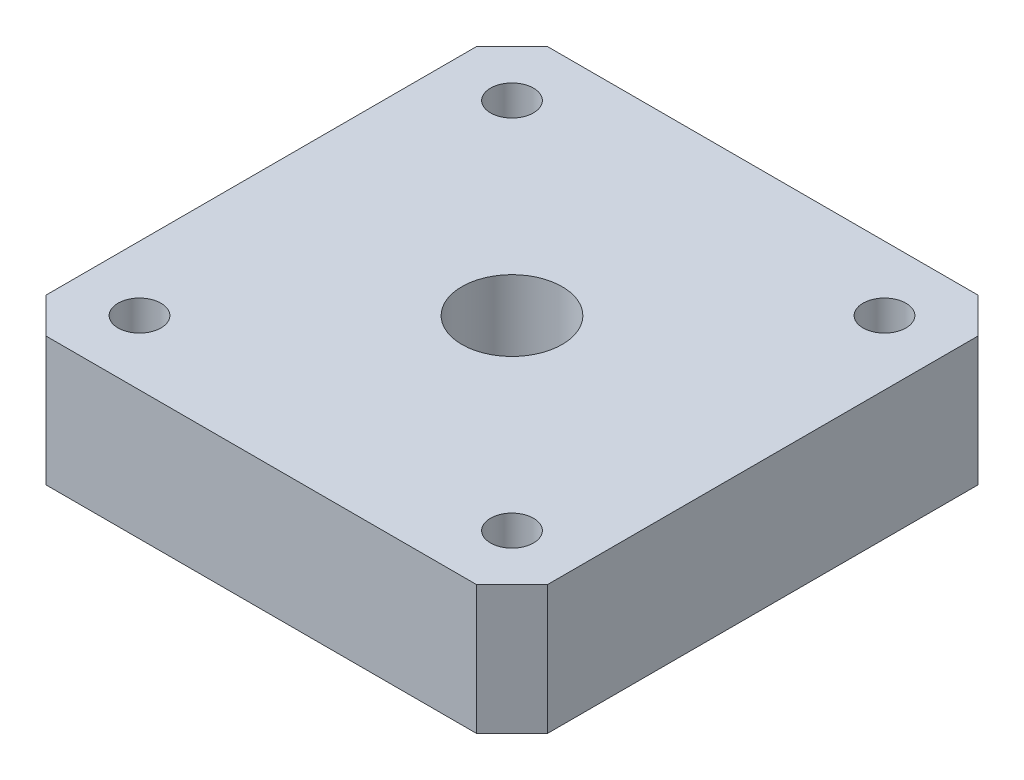
SolidWorks part; units mm, degrees
material "Aleación 1060"
ref_plane "Alzado" through (0, 0, 0) normal (0, 0, 1) x (1, 0, 0)
ref_plane "Planta" through (0, 0, 0) normal (0, 1, 0) x (1, 0, 0)
ref_plane "Vista lateral" through (0, 0, 0) normal (1, 0, 0) x (0, 0, -1)
sketch "Croquis1" plane through (0, 0, 0) normal (0, 1, 0) x (1, 0, 0)
  line L0 (0, 2.4731) -> (2.4731, 0)
  line L1 (2.4731, 0) -> (32.5269, 0)
  line L2 (32.5269, 0) -> (35, 2.4731)
  line L3 (35, 2.4731) -> (35, 32.5269)
  line L4 (35, 32.5269) -> (32.5269, 35)
  line L5 (32.5269, 35) -> (2.4731, 35)
  line L6 (2.4731, 35) -> (0, 32.5269)
  line L7 (0, 32.5269) -> (0, 2.4731)
  dimension "D1" = 35
  dimension "D2" = 35
  dimension "D3" = 46
  dimension "D4" = 46
  dimension "D5" = 45
extrude "Saliente-Extruir1" add sketch "Croquis1" along normal blind 9
sketch "Croquis2" plane through (0, 9, 0) normal (0, 1, 0) x (1, 0, 0)
  line L0 (17.5, 35) -> (17.5, 0) construction
  line L1 (32.5269, 35) -> (2.4731, 35) construction
  line L2 (2.4731, 0) -> (32.5269, 0) construction
  circle A0 centre (17.5, 17.5) radius 3.5
  dimension "D1" = 7
extrude "Cortar-Extruir1" cut sketch "Croquis2" against normal through all
sketch "Croquis3" plane through (0, 9, 0) normal (0, 1, 0) x (1, 0, 0)
  line L0 (4.5, 30.5) -> (30.5, 4.5) construction
  line L1 (4.5, 30.5) -> (30.5, 30.5) construction
  line L2 (4.5, 30.5) -> (4.5, 4.5) construction
  line L3 (4.5, 4.5) -> (30.5, 4.5) construction
  line L4 (30.5, 30.5) -> (30.5, 4.5) construction
  line L5 (4.5, 4.5) -> (30.5, 30.5) construction
  circle A0 centre (4.5, 30.5) radius 1.5
  circle A1 centre (30.5, 30.5) radius 1.5
  circle A2 centre (30.5, 4.5) radius 1.5
  circle A3 centre (4.5, 4.5) radius 1.5
  point P4 (17.5, 17.5)
  point P5 (17.5, 17.5)
  point P17 (17.5, 17.5)
  dimension "D3" = 3
  dimension "D1" = 26
  dimension "D2" = 26
  dimension "D4" = 4
extrude "Cortar-Extruir2" cut sketch "Croquis3" against normal through all
